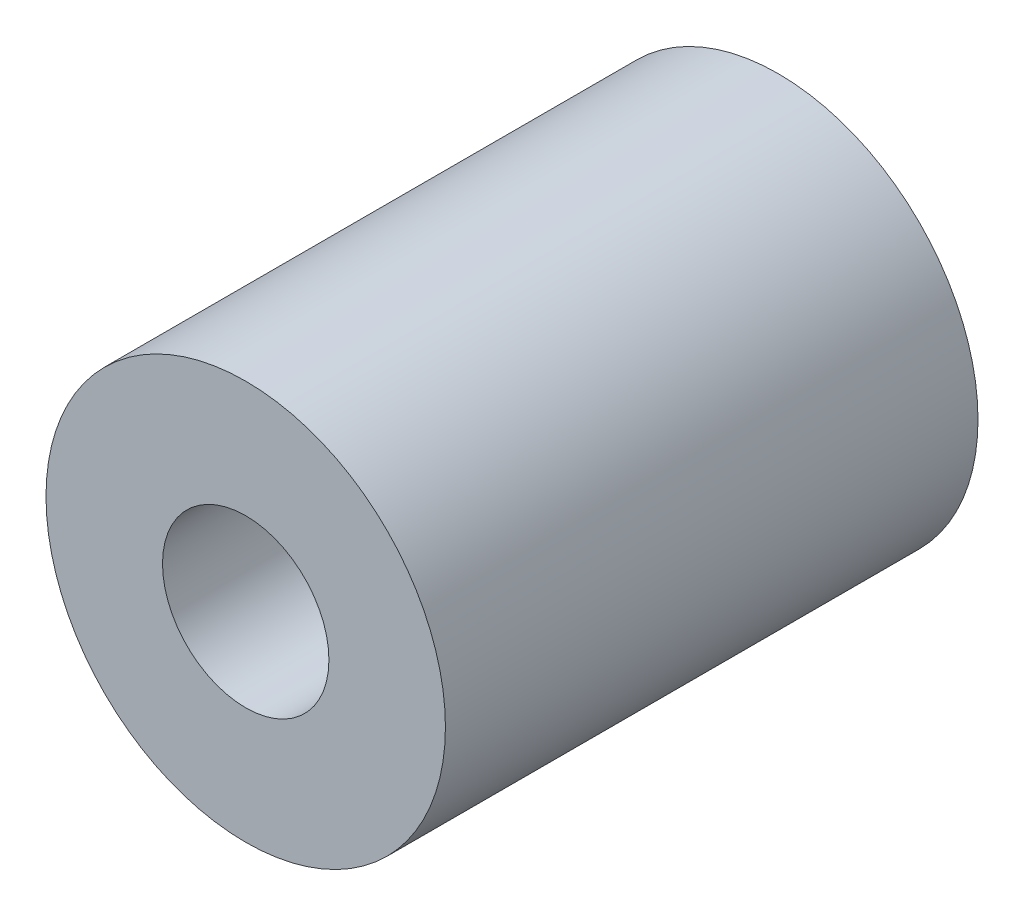
SolidWorks part; units mm, degrees
material "1060 Alloy"
ref_plane "Front Plane" through (0, 0, 0) normal (0, 0, 1) x (1, 0, 0)
ref_plane "Top Plane" through (0, 0, 0) normal (0, 1, 0) x (1, 0, 0)
ref_plane "Right Plane" through (0, 0, 0) normal (1, 0, 0) x (0, 0, -1)
sketch "Sketch1" plane through (0, 0, 0) normal (0, 0, 1) x (1, 0, 0)
  circle A0 centre (0, 0) radius 7.62
  circle A1 centre (0, 0) radius 3.175
  dimension "D1" = 15.24
  dimension "D2" = 6.35
extrude "Boss-Extrude1" add sketch "Sketch1" along normal blind 20.32
